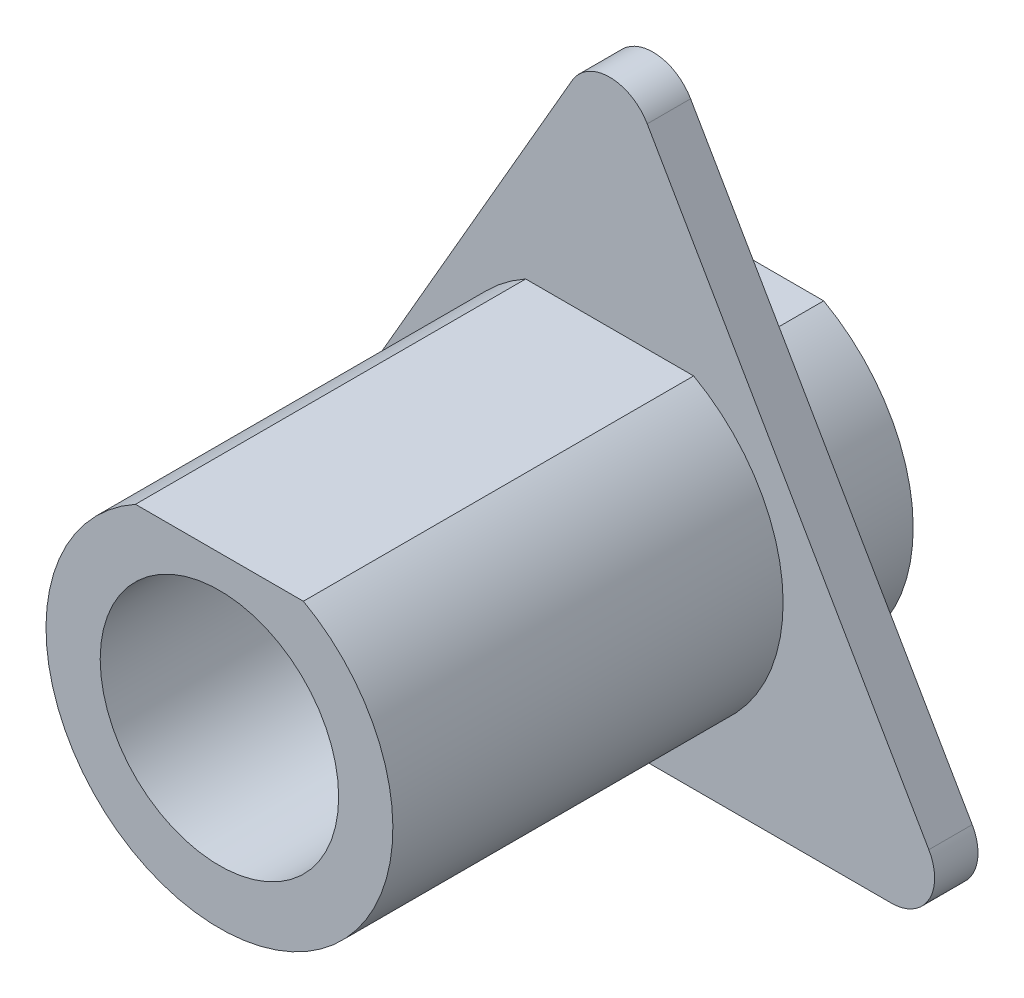
SolidWorks part; units mm, degrees
ref_plane "前视基准面" through (0, 0, 0) normal (0, 0, 1) x (1, 0, 0)
ref_plane "上视基准面" through (0, 0, 0) normal (0, 1, 0) x (1, 0, 0)
ref_plane "右视基准面" through (0, 0, 0) normal (1, 0, 0) x (0, 0, -1)
sketch "草图1" plane through (0, 0, 0) normal (0, 0, 1) x (1, 0, 0)
  line L0 (-1.9365, 3.5) -> (1.9365, 3.5)
  arc A0 (-1.9365, 3.5) -> (1.9365, 3.5) centre (0, 0) ccw
  dimension "D1" = 8
  dimension "D2" = 3.5
extrude "凸台-拉伸1" add sketch "草图1" along normal blind 12
ref_plane "基准面1" through (0, 0, 3) normal (0, 0, 1) x (1, 0, 0)
sketch "草图3" plane through (0, 0, 3) normal (0, 0, 1) x (1, 0, 0)
  line L4 (-6.4952, -4.75) -> (6.4952, -4.75)
  line L5 (7.3612, -3.25) -> (0.866, 8)
  line L6 (-0.866, 8) -> (-7.3612, -3.25)
  line L7 (0, 7.5) -> (0, 0) construction
  arc A0 (-7.3612, -3.25) -> (-6.4952, -4.75) centre (-6.4952, -3.75) ccw
  arc A1 (6.4952, -4.75) -> (7.3612, -3.25) centre (6.4952, -3.75) ccw
  arc A2 (0.866, 8) -> (-0.866, 8) centre (0, 7.5) ccw
extrude "凸台-拉伸2" add sketch "草图3" against normal blind 1
sketch "草图2" plane through (0, 0, 12) normal (0, 0, 1) x (1, 0, 0)
  circle A0 centre (0, 0) radius 2.75
  dimension "D1" = 5.5
extrude "切除-拉伸1" cut sketch "草图2" against normal blind 100
